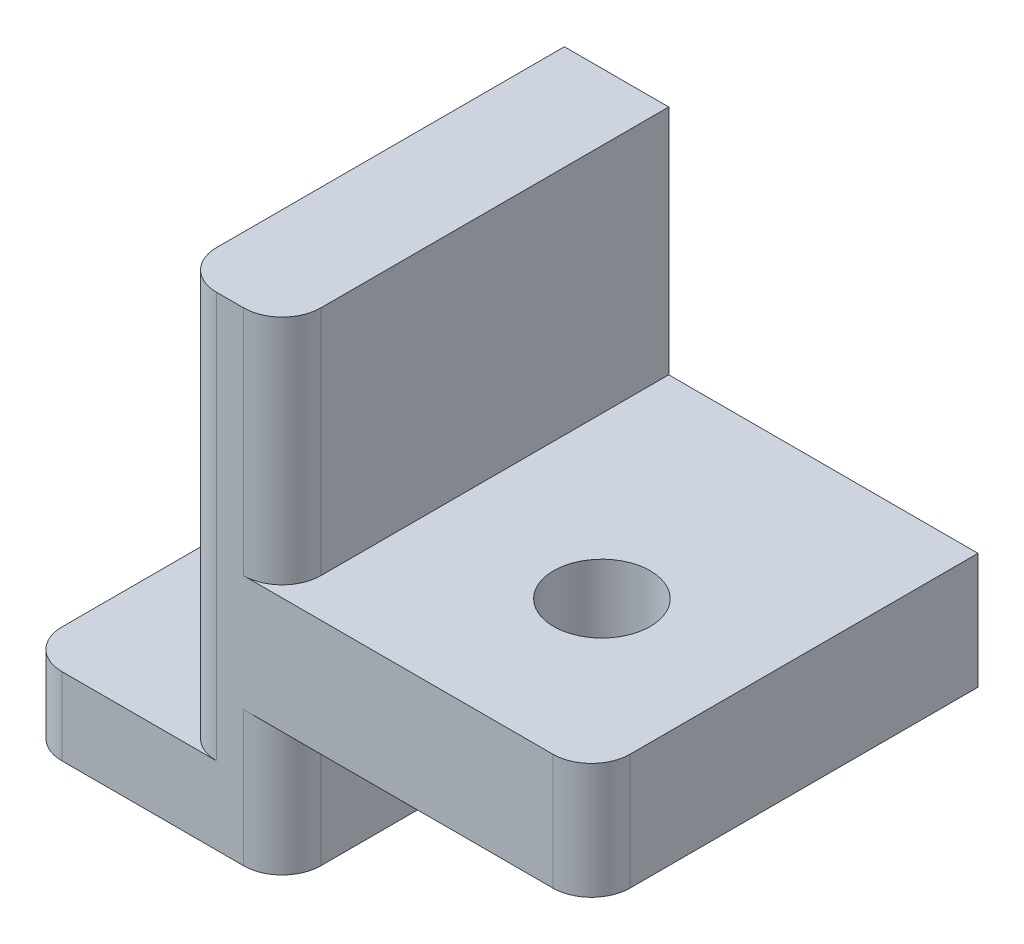
SolidWorks part; units mm, degrees
ref_plane "Ebene vorne" through (0, 0, 0) normal (0, 0, 1) x (1, 0, 0)
ref_plane "Ebene oben" through (0, 0, 0) normal (0, 1, 0) x (1, 0, 0)
ref_plane "Ebene rechts" through (0, 0, 0) normal (1, 0, 0) x (0, 0, -1)
sketch "Skizze1" plane through (0, 0, 0) normal (0, 0, 1) x (1, 0, 0)
  line L0 (-2.7, 6) -> (0, 6)
  line L1 (0, 6) -> (0, 0)
  line L2 (0, 0) -> (8, 0)
  line L3 (8, 0) -> (8, -3)
  line L4 (8, -3) -> (0, -3)
  line L5 (0, -3) -> (0, -6.5)
  line L6 (0, -6.5) -> (-6.7, -6.5)
  line L7 (-6.7, -6.5) -> (-6.7, -4.5)
  line L8 (-6.7, -4.5) -> (-2.7, -4.5)
  line L9 (-2.7, -4.5) -> (-2.7, 6)
  dimension "D1" = 2.7
  dimension "D2" = 6
  dimension "D3" = 3
  dimension "D4" = 4.5
  dimension "D5" = 2
  dimension "D6" = 4
  dimension "D7" = 8
extrude "Aufsatz-Linear austragen1" add sketch "Skizze1" along normal blind 10
hole_wizard "Ø2.5 (2.5) Durchmesser Bohrung1" positions "Skizze2" profile "Skizze3" hole size "Ø2.5" standard "ANSI Metrisch"
sketch "Skizze2" plane through (0, -3, 0) normal (0, -1, 0) x (-1, 0, 0)
  line L0 (0, -10) -> (0, 0) construction
  point P0 (-4.15, -5.8795)
  dimension "D1" = 4.15
sketch "Skizze3" plane through (4.15, -3, 5.8795) normal (1, 0, 0) x (0, 0, -1)
  line L0 (0, 0) -> (0, 5.7511)
  line L1 (0, 5.7511) -> (1.25, 5)
  line L2 (1.25, 5) -> (1.25, 0)
  line L5 (1.25, 0) -> (0, 0)
  line L10 (0, 5.7511) -> (-1.25, 5) construction
  line L11 (0, -6.35) -> (0, 107.95) construction
  dimension "Bohrerdurchmesser" = 2.5
  dimension "Bohrungstiefe" = 5
  dimension "Spitzenwinkel" = 118
fillet "Verrundung1" radius 1 4 edges at (0, 3, 10) (0, -4.75, 10) (8, -1.5, 10) (-6.7, -5.5, 10)
fillet "Verrundung2" radius 1 1 edges at (-2.7, 0.75, 10)
